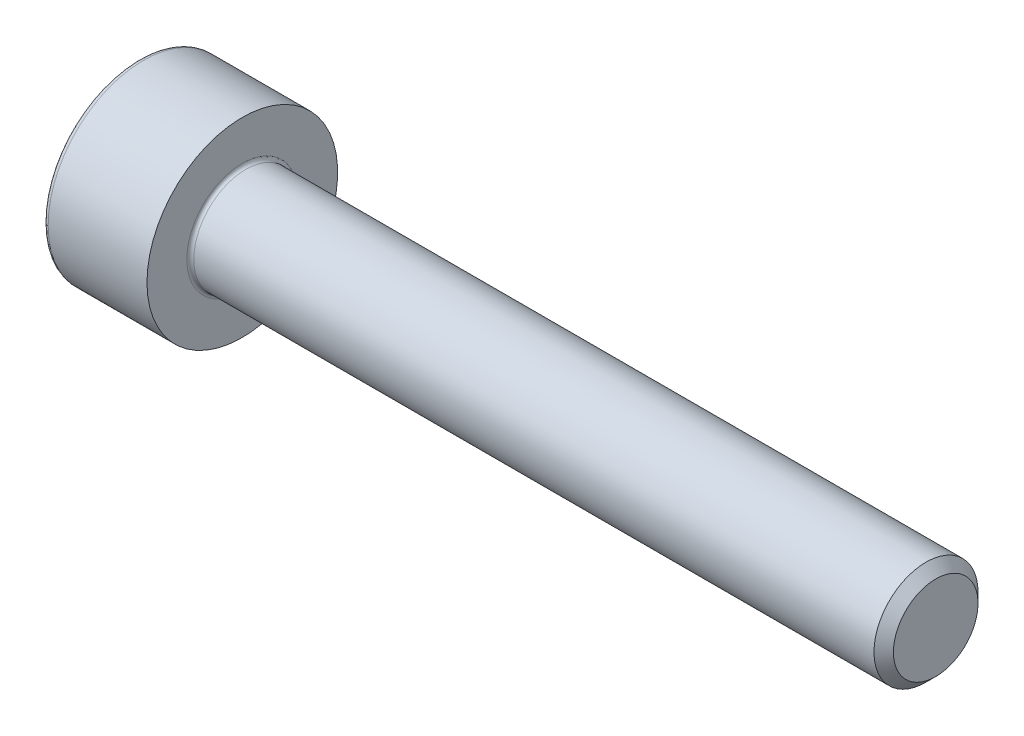
SolidWorks part; units mm, degrees
revolve "Base-Revolve" add sketch "BodySke"
sketch "BodySke" plane through (0, 0, 0) normal (0, 0, 1) x (1, 0, 0)
  line L0 (0, 0) -> (0, 2.75)
  line L1 (0, 2.75) -> (3, 2.75)
  line L2 (3, 2.75) -> (3, 1.5)
  line L3 (3, 1.5) -> (22.7195, 1.5)
  line L4 (23, 1.2195) -> (23, 0)
  line L5 (23, 0) -> (0, 0)
  line L6 (-31.75, 0) -> (127, 0) construction
  line L8 (23, 1.2195) -> (22.7195, 1.5)
  line L10 (23, -1.2195) -> (22.7195, -1.5) construction
  line L11 (3.5, 9.525) -> (3.5, 3.175) construction
  line L12 (18, 9.525) -> (18, 3.175) construction
  line L13 (-37, 9.525) -> (-37, 3.175) construction
  dimension "Head_ht" = 3
  dimension "Length" = 20
  dimension "Body_ch_ang" = 45
  dimension "Diameter" = 3
  dimension "Minor_dia" = 2.439
  dimension "Advance" = 0.5
  dimension "Thread_nom" = 5
  dimension "Thread_length" = 60
  dimension "Head_dia" = 5.5
cosmetic thread "ThreadCosmetic" [suppressed]
fillet "Fillet1" radius 0.1 1 edges at (3, 0, 1.5)
fillet "Fillet2" radius 0.15 1 edges at (0, 0, 2.75)
ref_plane "Plane1" through (0, 0, 0) normal (0, 0, 1) x (1, 0, 0)
ref_plane "Plane2" through (0, 0, 0) normal (0, 1, 0) x (1, 0, 0)
ref_plane "Plane3" through (0, 0, 0) normal (1, 0, 0) x (0, 0, -1)
sketch "Sketch2" plane through (0, 0, 0) normal (0, 0, 1) x (1, 0, 0)
  line L0 (0, 1.28) -> (1.3, 1.28)
  line L1 (1.3, 1.28) -> (2.039, 0)
  line L2 (-31.75, 0) -> (127, 0) construction
  line L3 (2.039, 0) -> (0, 0)
  line L4 (0, 0) -> (0, 1.28)
  line L6 (0, 0) -> (47.625, 0) construction
  dimension "D1" = 1.28
  dimension "D2" = 60
  dimension "Depth" = 1.3
revolve "Hex-PreBroach" cut sketch "Sketch2" angle 360 about L6
sketch "Sketch3" plane through (0, 0, 0) normal (-1, 0, 0) x (0, 0.5, 0.866)
  line L0 (0.739, 1.28) -> (-0.739, 1.28)
  line L1 (-0.739, 1.28) -> (-1.478, 0)
  line L2 (0.739, 1.28) -> (1.478, 0)
  line L3 (0.739, -1.28) -> (1.478, 0)
  line L4 (0.739, -1.28) -> (-0.739, -1.28)
  line L5 (-0.739, -1.28) -> (-1.478, 0)
  dimension "D1" = 1.28
  dimension "D2" = 1.28
  dimension "Hex_size" = 2.56
extrude "Hex" cut sketch "Sketch3" against normal blind 1.3
sketch "ThdSchSke" plane through (0, 0, 0) normal (0, 0, 1) x (1, 0, 0)
  line L0 (18, -1.2195) -> (17.8036, -1.5)
  line L1 (18, -1.2195) -> (18.1964, -1.5)
  line L2 (18.1964, -1.5) -> (18.1964, -1.875)
  line L3 (-3.175, 0) -> (5.1513, 0) construction
  line L4 (0, 2.6) -> (0, -2.6) construction
  line L5 (18.1964, -1.875) -> (17.8036, -1.875)
  line L6 (17.8036, -1.875) -> (17.8036, -1.5)
  dimension "Thread_minor" = 2.439
  dimension "Diameter" = 3
  dimension "Start" = 18
revolve "ThreadSchematic" [suppressed] cut sketch "ThdSchSke" angle 360 about L3
pattern_linear "ThdSchPat" [suppressed]
equation "\"D2@Sketch3\" = \"Hex_size@Sketch3\" / 2"
equation "\"D1@Sketch3\" = \"Hex_size@Sketch3\" / 2"
equation "\"D1@Sketch2\" = \"Hex_size@Sketch3\" / 2"
equation "\"Thread_minor@ThreadCosmetic\"  =  \"Minor_dia@BodySke\""
equation "\"Depth@Sketch2\" =  \"Key_eng@Hex\""
equation "\"Thread_length@ThreadCosmetic\" = ((sgn( (\"Length@BodySke\" - \"Advance@BodySke\" * 3.0) - \"Thread_nom@BodySke\" )-1)*( (\"Length@BodySke\" - \"Advance@BodySke\" * 3.0) - \"Thread_nom@BodySke\" ))/-2+ \"Thread_nom@BodySke\""
equation "\"Thread_minor@ThdSchSke\" = \"Minor_dia@BodySke\""
equation "\"Diameter@ThdSchSke\" = \"Diameter@BodySke\""
equation "\"Overcut@ThdSchSke\" = \"Diameter@BodySke\" * 1.25"
equation "\"Start@ThdSchSke\" = \"Head_ht@BodySke\" + \"Length@BodySke\" - \"Thread_length@ThreadCosmetic\"  '---Non-countersunk---"
equation "\"Num_threads@ThdSchPat\" = int( \"Thread_length@ThreadCosmetic\" / \"Advance@BodySke\" + 0.999 )  + 1"
equation "\"Advance@ThdSchPat\" = \"Thread_length@ThreadCosmetic\" /  (\"Num_threads@ThdSchPat\" - 1) 'relax it"
equation "\"Num_threads@ThdSchPat\" = \"Num_threads@ThdSchPat\" - sgn( \"Num_threads@ThdSchPat\" - 1) '---chamfered tips only---"
